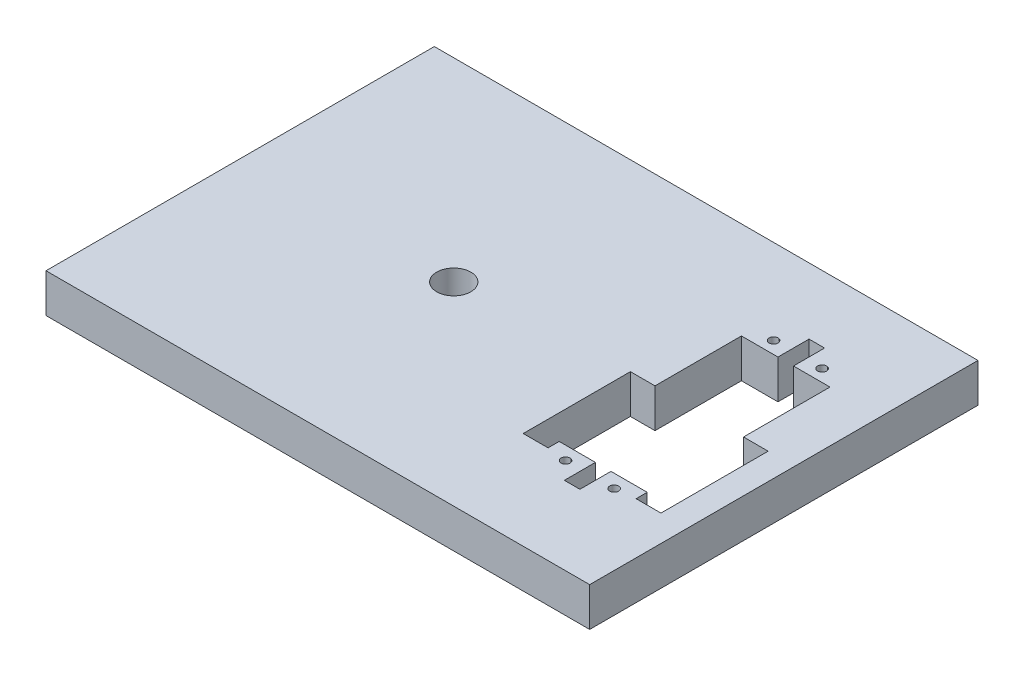
SolidWorks part; units mm, degrees
material "Pine"
ref_plane "Front Plane" through (0, 0, 0) normal (0, 0, 1) x (1, 0, 0)
ref_plane "Top Plane" through (0, 0, 0) normal (0, 1, 0) x (1, 0, 0)
ref_plane "Right Plane" through (0, 0, 0) normal (1, 0, 0) x (0, 0, -1)
sketch "Sketch1" plane through (0, 0, 0) normal (0, 1, 0) x (1, 0, 0)
  line L0 (-88.9, 0) -> (88.9, 0) construction
  line L1 (-88.9, 63.5) -> (88.9, 63.5)
  line L2 (-88.9, 63.5) -> (-88.9, -63.5)
  line L3 (-88.9, -63.5) -> (88.9, -63.5)
  line L4 (88.9, 63.5) -> (88.9, -63.5)
  line L5 (-88.9, 63.5) -> (88.9, -63.5) construction
  line L6 (-88.9, -63.5) -> (88.9, 63.5) construction
  line L7 (57.7631, -14.0454) -> (26.0047, -14.0454) construction
  line L8 (26.0047, -14.0454) -> (39.4751, -27.5158) construction
  line L9 (26.0047, -14.0454) -> (39.4751, -0.575) construction
  line L10 (57.7631, -37.8579) -> (57.7631, -14.0454) construction
  line L11 (43.2851, -27.936) -> (72.2411, -27.936)
  line L12 (43.2851, -27.936) -> (43.2851, 31.754)
  line L13 (43.2851, 31.754) -> (72.2411, 31.754)
  line L14 (72.2411, -27.936) -> (72.2411, 31.754)
  circle A0 centre (-19.05, 0) radius 5.588
  circle A1 centre (49.8256, -32.3017) radius 1.4605
  circle A2 centre (65.7006, -32.3017) radius 1.4605
  circle A3 centre (49.8256, 35.7195) radius 1.4605
  circle A4 centre (65.7006, 35.7195) radius 1.4605
  point P16 (76.0511, -27.5158)
  point P17 (76.0511, -0.575)
  dimension "D4" = 11.176
  dimension "D1" = 177.8
  dimension "D2" = 127
  dimension "D3" = 69.85
extrude "Boss-Extrude1" add sketch "Sketch1" along normal blind 12.7
sketch "Sketch3" plane through (0, 0, 0) normal (0, 1, 0) x (1, 0, 0)
  line L0 (35.238, -14.0454) -> (80.2881, -14.0454) construction
  line L1 (35.238, 3.4806) -> (43.366, 3.4806)
  line L2 (35.238, 3.4806) -> (35.238, -31.5714)
  line L3 (35.238, -31.5714) -> (43.366, -31.5714)
  line L4 (43.366, 3.4806) -> (43.366, -31.5714)
  line L5 (35.238, 3.4806) -> (43.366, -31.5714) construction
  line L6 (35.238, -31.5714) -> (43.366, 3.4806) construction
  line L7 (72.1601, 3.4806) -> (80.2881, 3.4806)
  line L8 (72.1601, 3.4806) -> (72.1601, -31.5714)
  line L9 (72.1601, -31.5714) -> (80.2881, -31.5714)
  line L10 (80.2881, 3.4806) -> (80.2881, -31.5714)
  line L11 (72.1601, 3.4806) -> (80.2881, -31.5714) construction
  line L12 (72.1601, -31.5714) -> (80.2881, 3.4806) construction
  line L13 (57.7631, -37.8579) -> (57.7631, -14.0454) construction
  line L14 (55.2231, -27.936) -> (60.3031, -27.936)
  line L15 (55.2231, -27.936) -> (55.2231, -38.096)
  line L16 (55.2231, -38.096) -> (60.3031, -38.096)
  line L17 (60.3031, -27.936) -> (60.3031, -38.096)
  line L18 (43.2851, -27.936) -> (72.2411, -27.936) construction
  line L19 (55.2231, 41.914) -> (60.3031, 41.914)
  line L20 (55.2231, 41.914) -> (55.2231, 31.754)
  line L21 (55.2231, 31.754) -> (60.3031, 31.754)
  line L22 (60.3031, 41.914) -> (60.3031, 31.754)
  line L23 (57.7631, -14.0454) -> (57.7631, 44.2541) construction
  line L24 (43.2851, 31.754) -> (72.2411, 31.754) construction
  point P9 (57.7631, -14.0454)
  dimension "D1" = 8.128
  dimension "D2" = 35.052
  dimension "D3" = 8.128
  dimension "D4" = 35.052
  dimension "D5" = 5.08
  dimension "D6" = 2.54
  dimension "D7" = 10.16
  dimension "D8" = 2.54
extrude "Cut-Extrude3" cut sketch "Sketch3" along normal through all
